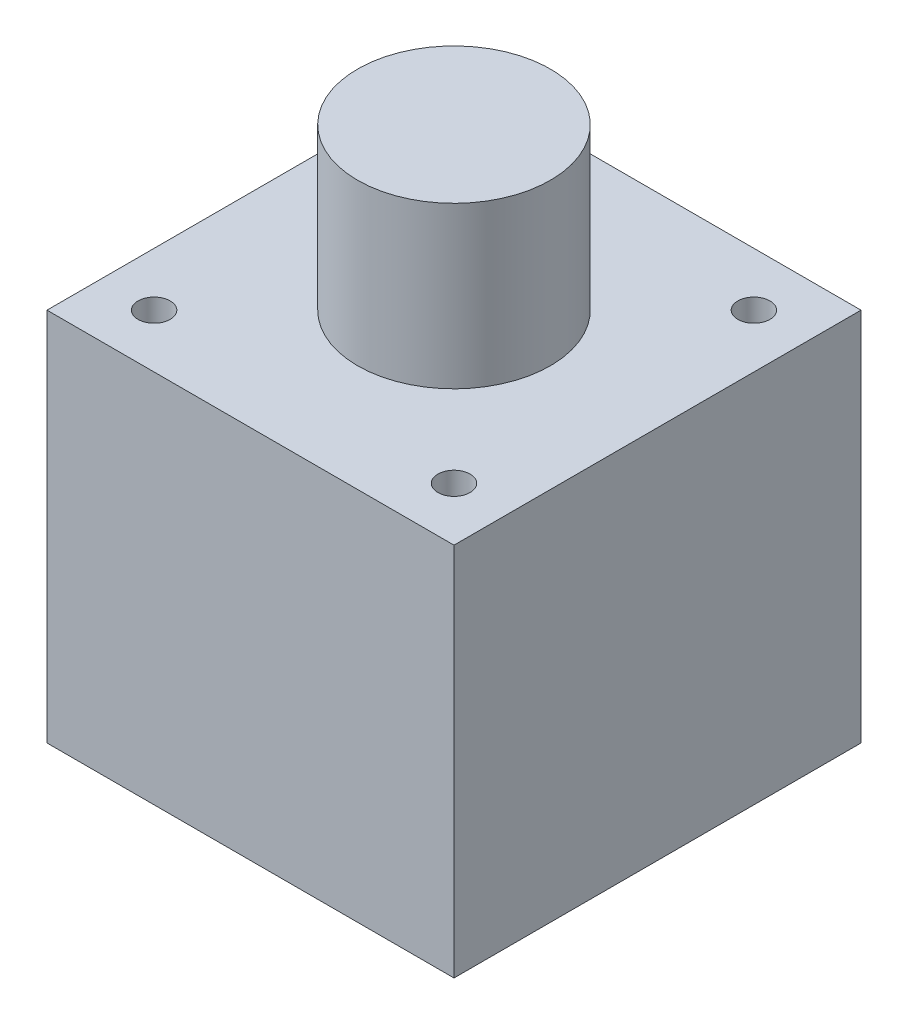
SolidWorks part; units mm, degrees
ref_plane "Front Plane" through (0, 0, 0) normal (0, 0, 1) x (1, 0, 0)
ref_plane "Top Plane" through (0, 0, 0) normal (0, 1, 0) x (1, 0, 0)
ref_plane "Right Plane" through (0, 0, 0) normal (1, 0, 0) x (0, 0, -1)
sketch "Sketch1" plane through (0, 0, 0) normal (0, 1, 0) x (1, 0, 0)
  line L1 (19, -19) -> (-19, -19)
  line L2 (19, -19) -> (19, 19)
  line L3 (19, 19) -> (-19, 19)
  line L4 (-19, -19) -> (-19, 19)
  line L5 (19, -19) -> (-19, 19) construction
  line L6 (19, 19) -> (-19, -19) construction
  point P0 (0, 0)
  dimension "D1" = 38
extrude "Boss-Extrude1" add sketch "Sketch1" along normal blind 35 contours L3 L4 L1 L2
sketch "Sketch2" plane through (0, 35, 0) normal (0, 1, 0) x (1, 0, 0)
  circle A0 centre (0, 0) radius 9
  dimension "D1" = 18
extrude "Boss-Extrude2" add sketch "Sketch2" along normal blind 15
hole_wizard "Ø3.0mm Dowel Hole1" positions "Sketch5" profile "Sketch3" hole size "Ø3.0" standard "ANSI Metric" end condition through all
sketch "Sketch5" plane through (0, 0, 0) normal (0, -1, 0) x (-1, 0, 0)
  line L0 (-19, -19) -> (19, 19) construction
  point P0 (-14, -14)
  point P18 (-14, 14)
  point P19 (14, 14)
  point P20 (14, -14)
  dimension "D1" = 14
  dimension "D2" = 4
sketch "Sketch3" plane through (14, 0, 14) normal (1, 0, 0) x (0, 0, -1)
  line L0 (0, 0) -> (0, 50)
  line L1 (0, 50) -> (1.5, 50)
  line L2 (1.5, 50) -> (1.5, 0)
  line L5 (1.5, 0) -> (0, 0)
  line L11 (0, -6.35) -> (0, 107.95) construction
  dimension "Thru Hole Dia." = 3
  dimension "Thru Hole Depth" = 50
